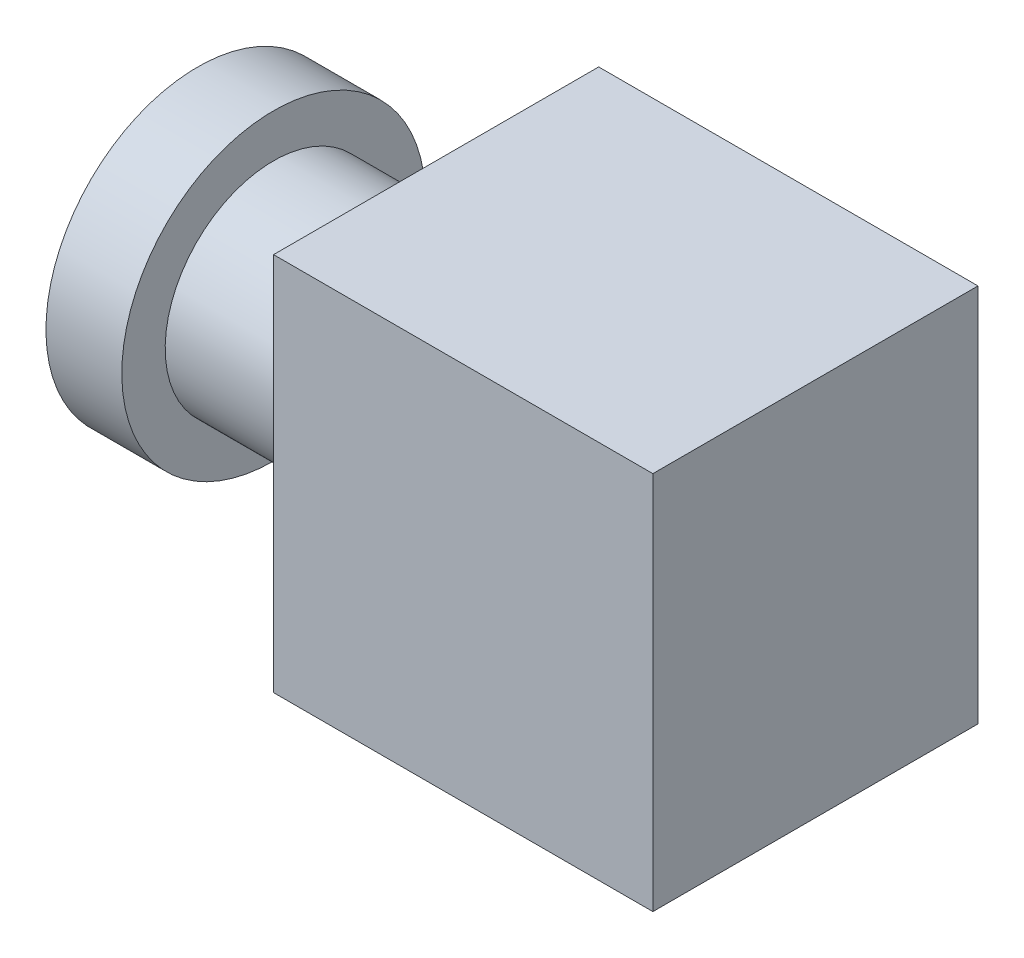
SolidWorks part; units mm, degrees
ref_plane "Front Plane" through (0, 0, 0) normal (0, 0, 1) x (1, 0, 0)
ref_plane "Top Plane" through (0, 0, 0) normal (0, 1, 0) x (1, 0, 0)
ref_plane "Right Plane" through (0, 0, 0) normal (1, 0, 0) x (0, 0, -1)
sketch "Sketch1" plane through (0, 0, 0) normal (0, 0, 1) x (1, 0, 0)
  line L1 (-17.5, 17.5) -> (17.5, 17.5)
  line L2 (-17.5, 17.5) -> (-17.5, -17.5)
  line L3 (-17.5, -17.5) -> (17.5, -17.5)
  line L4 (17.5, 17.5) -> (17.5, -17.5)
  line L5 (-17.5, 17.5) -> (17.5, -17.5) construction
  line L6 (-17.5, -17.5) -> (17.5, 17.5) construction
  point P0 (0, 0)
  dimension "D1" = 35
  dimension "D2" = 35
extrude "Boss-Extrude1" add sketch "Sketch1" along normal blind 30
sketch "Sketch2" plane through (-17.5, 0, 0) normal (-1, 0, 0) x (0, 0, 1)
  circle A0 centre (15, 0) radius 10
  dimension "D1" = 20
extrude "Boss-Extrude2" add sketch "Sketch2" along normal blind 15
sketch "Sketch3" plane through (-32.5, 0, 0) normal (-1, 0, 0) x (0, 0, 1)
  circle A0 centre (15, 0) radius 14
  dimension "D1" = 28
extrude "Boss-Extrude3" add sketch "Sketch3" along normal blind 7
